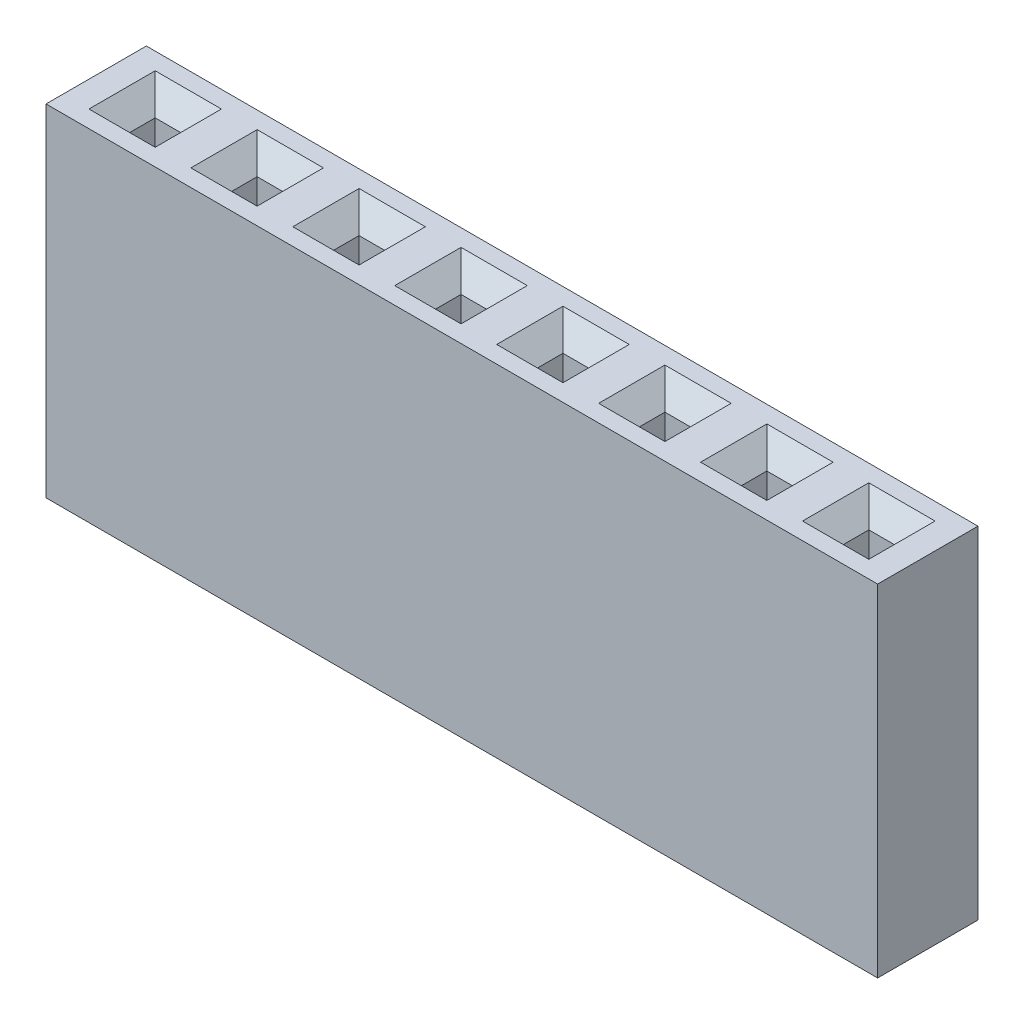
SolidWorks part; units mm, degrees
material "ABS PC"
ref_plane "Front Plane" through (0, 0, 0) normal (0, 0, 1) x (1, 0, 0)
ref_plane "Top Plane" through (0, 0, 0) normal (0, 1, 0) x (1, 0, 0)
ref_plane "Right Plane" through (0, 0, 0) normal (1, 0, 0) x (0, 0, -1)
sketch "Sketch1" plane through (0, 0, 0) normal (0, 1, 0) x (1, 0, 0)
  line L1 (0, 0) -> (20.72, 0)
  line L2 (0, 0) -> (0, 2.5)
  line L3 (0, 2.5) -> (20.72, 2.5)
  line L4 (20.72, 0) -> (20.72, 2.5)
  dimension "D1" = 2.5
  dimension "D2" = 20.72
extrude "Boss-Extrude1" add sketch "Sketch1" along normal blind 8.5
sketch "Sketch2" plane through (0, 8.5, 0) normal (0, 1, 0) x (1, 0, 0)
  line L0 (0, 0) -> (20.72, 0) construction
  line L1 (1.1525, 1.5675) -> (1.7875, 1.5675)
  line L2 (1.1525, 1.5675) -> (1.1525, 0.9325)
  line L3 (1.1525, 0.9325) -> (1.7875, 0.9325)
  line L4 (1.7875, 1.5675) -> (1.7875, 0.9325)
  line L5 (1.1525, 1.5675) -> (1.7875, 0.9325) construction
  line L6 (1.1525, 0.9325) -> (1.7875, 1.5675) construction
  line L7 (0, 2.5) -> (0, 0) construction
  point P0 (1.47, 1.25)
  dimension "D1" = 0.635
  dimension "D2" = 0.635
  dimension "D3" = 1.25
  dimension "D4" = 1.47
extrude "Cut-Extrude1" cut sketch "Sketch2" against normal blind 6.35
chamfer "Chamfer1" distance 0.508 angle 45 4 edges at (1.1525, 8.5, -1.25) (1.47, 8.5, -0.9325) (1.7875, 8.5, -1.25) (1.47, 8.5, -1.5675)
pattern_linear "LPattern1" count 8 spacing 2.54 along (1, 0, 0) of "Cut-Extrude1", "Chamfer1"
